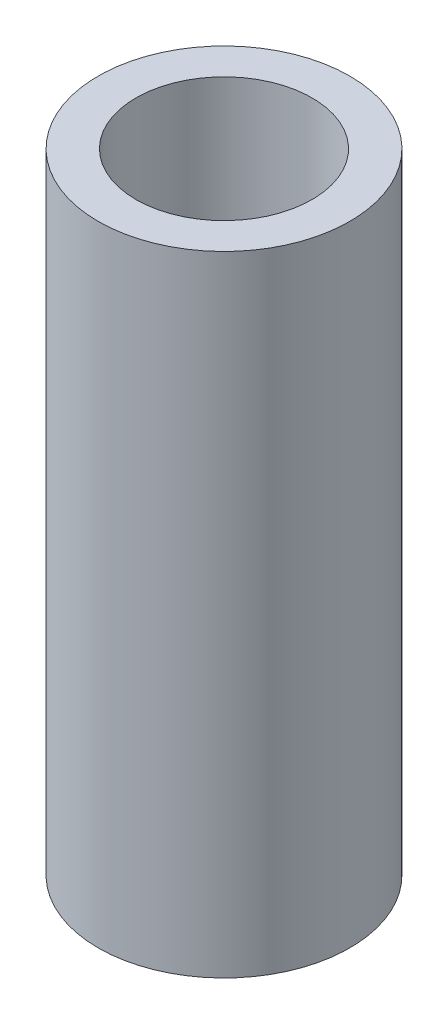
SolidWorks part; units mm, degrees
material "Plain Carbon Steel"
ref_plane "Front Plane" through (0, 0, 0) normal (0, 0, 1) x (1, 0, 0)
ref_plane "Top Plane" through (0, 0, 0) normal (0, 1, 0) x (1, 0, 0)
ref_plane "Right Plane" through (0, 0, 0) normal (1, 0, 0) x (0, 0, -1)
sketch "Sketch1" plane through (0, 0, 0) normal (0, 1, 0) x (1, 0, 0)
  circle A0 centre (0, 0) radius 10
  dimension "D1" = 20
extrude "Boss-Extrude1" add sketch "Sketch1" along normal blind 50
sketch "Sketch2" plane through (0, 50, 0) normal (0, 1, 0) x (1, 0, 0)
  circle A0 centre (0, 0) radius 4
  dimension "D1" = 8
extrude "Cut-Extrude1" cut sketch "Sketch2" against normal through all
sketch "Sketch3" plane through (0, 50, 0) normal (0, 1, 0) x (1, 0, 0)
  circle A0 centre (0, 0) radius 7
  dimension "D1" = 14
extrude "Cut-Extrude2" cut sketch "Sketch3" against normal blind 35
